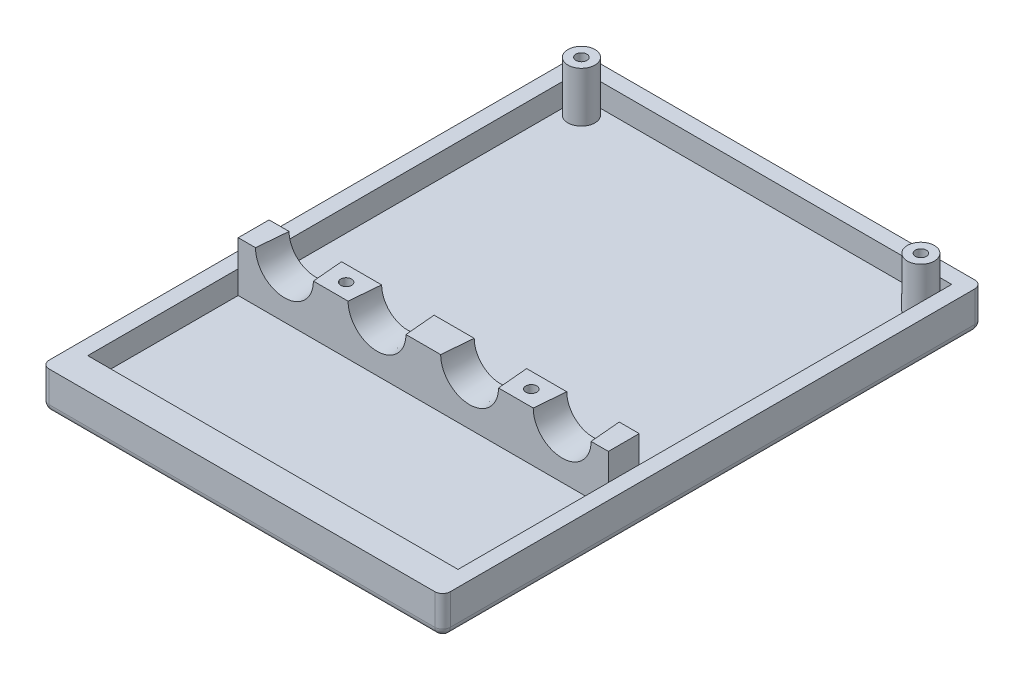
SolidWorks part; units mm, degrees
ref_plane "Front Plane" through (0, 0, 0) normal (0, 0, 1) x (1, 0, 0)
ref_plane "Top Plane" through (0, 0, 0) normal (0, 1, 0) x (1, 0, 0)
ref_plane "Right Plane" through (0, 0, 0) normal (1, 0, 0) x (0, 0, -1)
sketch "Sketch1" plane through (0, 0, 0) normal (0, 1, 0) x (1, 0, 0)
  line L1 (-41.275, -55.5625) -> (41.275, -55.5625)
  line L2 (-41.275, -55.5625) -> (-41.275, 55.5625)
  line L3 (-41.275, 55.5625) -> (41.275, 55.5625)
  line L4 (41.275, -55.5625) -> (41.275, 55.5625)
  line L5 (-41.275, -55.5625) -> (41.275, 55.5625) construction
  line L6 (-41.275, 55.5625) -> (41.275, -55.5625) construction
  point P0 (0, 0)
  dimension "D1" = 111.125
  dimension "D2" = 82.55
extrude "Boss-Extrude1" add sketch "Sketch1" along normal blind 7.9375
sketch "Sketch3" plane through (0, 7.9375, 0) normal (0, 1, 0) x (-1, 0, 0)
  line L0 (0, 0) -> (0, -1.5875) construction
  line L2 (38.1, 49.2125) -> (-38.1, 49.2125)
  line L3 (38.1, 49.2125) -> (38.1, -52.3875)
  line L4 (38.1, -52.3875) -> (-38.1, -52.3875)
  line L5 (-38.1, 49.2125) -> (-38.1, -52.3875)
  line L6 (38.1, 49.2125) -> (-38.1, -52.3875) construction
  line L7 (38.1, -52.3875) -> (-38.1, 49.2125) construction
  dimension "D1" = 1.5875
  dimension "D2" = 101.6
  dimension "D3" = 76.2
extrude "Cut-Extrude1" cut sketch "Sketch3" against normal offset from surface (4.7625 mm away) 3.175 up to face at (0, 0, 0)
sketch "Sketch4" plane through (0, 3.175, 0) normal (0, 1, 0) x (-1, 0, 0)
  line L0 (0, 49.2125) -> (0, 18.2563) construction
  line L1 (38.1, 49.2125) -> (-38.1, 49.2125) construction
  line L2 (38.1, 18.2563) -> (-38.1, 18.2563)
  line L3 (38.1, 18.2563) -> (38.1, 11.9063)
  line L4 (-38.1, 18.2563) -> (-38.1, 11.9063)
  line L5 (38.1, 11.9063) -> (-38.1, 11.9063)
  line L6 (38.1, -52.3875) -> (38.1, 49.2125) construction
  line L7 (-38.1, 49.2125) -> (-38.1, -52.3875) construction
  line L8 (0, -52.3875) -> (0, 11.9063) construction
  line L9 (-38.1, -52.3875) -> (38.1, -52.3875) construction
  line L10 (38.1, -52.3875) -> (38.1, 49.2125) construction
  line L11 (-38.1, -52.3875) -> (38.1, -52.3875) construction
  circle A0 centre (34.925, -49.2125) radius 2.7781
  circle A1 centre (-34.925, -49.2125) radius 2.7781
  dimension "D5" = 5.5562
  dimension "D1" = 30.9562
  dimension "D2" = 6.35
  dimension "D3" = 3.175
  dimension "D4" = 3.175
extrude "Boss-Extrude2" add sketch "Sketch4" along normal blind 4.7625
sketch "Sketch5" plane through (0, 7.9375, 0) normal (0, 1, 0) x (-1, 0, 0)
  line L0 (0, 11.9063) -> (0, 18.2563) construction
  line L1 (-38.1, 11.9063) -> (38.1, 11.9062) construction
  line L2 (38.1, 18.2563) -> (-38.1, 18.2563) construction
  line L3 (-38.1, 11.9062) -> (38.1, 11.9062) construction
  line L4 (38.0873, 18.2563) -> (-38.0873, 18.2563)
  line L5 (38.0873, 18.2563) -> (38.0873, 11.9062)
  line L6 (38.0873, 11.9062) -> (-38.0873, 11.9062)
  line L7 (-38.0873, 18.2563) -> (-38.0873, 11.9062)
  line L8 (38.0873, 18.2563) -> (-38.0873, 11.9062) construction
  line L9 (38.0873, 11.9062) -> (-38.0873, 18.2563) construction
  circle A0 centre (34.925, -49.2125) radius 2.7781
  circle A1 centre (-34.925, -49.2125) radius 2.7781
  point P6 (0, 15.0813)
  point P7 (0, 15.0813)
  dimension "D1" = 76.1746
extrude "Boss-Extrude3" add sketch "Sketch5" along normal blind 5.5499
sketch "Sketch6" plane through (0, 13.4874, 0) normal (0, 1, 0) x (-1, 0, 0)
  line L0 (0, 11.9062) -> (0, 18.2563) construction
  line L1 (-38.1, 11.9062) -> (38.1, 11.9062) construction
  line L2 (38.0873, 18.2563) -> (-38.0873, 18.2563) construction
  point P6 (0, 15.0813)
  point P7 (-9.525, 15.0813)
  point P8 (-28.575, 15.0813)
  point P9 (9.525, 15.0813)
  point P10 (28.575, 15.0813)
  dimension "D1" = 9.525
  dimension "D2" = 19.05
  dimension "D3" = 9.525
  dimension "D4" = 19.05
sketch "Sketch7" plane through (0, 0, 18.2563) normal (0, 0, 1) x (1, 0, 0)
  circle A0 centre (-28.575, 13.4874) radius 5.9531
  circle A1 centre (-9.525, 13.4874) radius 5.9531
  circle A2 centre (9.525, 13.4874) radius 5.9531
  circle A3 centre (28.575, 13.4874) radius 5.9531
  dimension "D1" = 11.9062
  dimension "D2" = 11.9062
  dimension "D3" = 11.9062
  dimension "D4" = 11.9062
extrude "Cut-Extrude2" cut sketch "Sketch7" against normal up to next (6.35 mm away) draft 5
fillet "Fillet1" radius 1.5875 8 edges at (-41.275, 0, 0) (-41.275, 3.9688, -55.5625) (0, 0, -55.5625) (41.275, 3.9688, -55.5625) (41.275, 0, 0) (41.275, 3.9688, 55.5625) (0, 0, 55.5625) (-41.275, 3.9688, 55.5625)
sketch "Sketch8"
sketch "Sketch9" plane through (0, 0, 0) normal (0, -1, 0) x (1, 0, 0)
  line L0 (-19.8716, 50.0609) -> (-23.3787, 50.0609)
  line L1 (-23.3787, 50.0609) -> (-23.3787, 49.463)
  line L2 (-23.3787, 49.463) -> (-24.789, 49.463)
  line L3 (-24.789, 49.463) -> (-24.789, 50.0609)
  line L4 (-24.789, 50.0609) -> (-28.2981, 50.0609)
  line L5 (-28.2981, 50.0609) -> (-28.2981, 49.463)
  line L6 (-28.2981, 49.463) -> (-30.1467, 49.463)
  line L7 (-30.1467, 49.463) -> (-30.1467, 48.2204)
  line L8 (-30.1467, 48.2204) -> (-30.8243, 48.2204)
  line L9 (-30.8243, 48.2204) -> (-30.8243, 47.5361)
  line L10 (-30.8243, 47.5361) -> (-31.942, 47.5361)
  line L11 (-31.942, 47.5361) -> (-31.942, 46.3625)
  line L12 (-31.942, 46.3625) -> (-32.6685, 46.3625)
  line L13 (-32.6685, 46.3625) -> (-32.6685, 45.7269)
  line L14 (-32.6685, 45.7269) -> (-33.2019, 45.7269)
  line L15 (-33.2019, 45.7269) -> (-33.2019, 43.2402)
  line L16 (-33.2019, 43.2402) -> (-33.7772, 43.2402)
  line L17 (-33.7772, 43.2402) -> (-33.7772, 42.0201)
  line L18 (-33.7772, 42.0201) -> (-36.2575, 42.0201)
  line L19 (-36.2575, 42.0201) -> (-36.2575, 41.5241)
  line L20 (-36.2575, 41.5241) -> (-36.8878, 41.5241)
  line L21 (-36.8878, 41.5241) -> (-36.8878, 37.8201)
  line L22 (-36.8878, 37.8201) -> (-36.2575, 37.8201)
  line L23 (-36.2575, 37.8201) -> (-36.2575, 37.3353)
  line L24 (-36.2575, 37.3353) -> (-34.4858, 37.3353)
  line L25 (-34.4858, 37.3353) -> (-34.4858, 32.325)
  line L26 (-34.4858, 32.325) -> (-33.7772, 32.325)
  line L27 (-33.7772, 32.325) -> (-33.7772, 31.6945)
  line L28 (-33.7772, 31.6945) -> (-33.2019, 31.6945)
  line L29 (-33.2019, 31.6945) -> (-33.2019, 30.5277)
  line L30 (-33.2019, 30.5277) -> (-31.942, 30.5277)
  line L31 (-31.942, 30.5277) -> (-31.942, 29.3143)
  line L32 (-31.942, 29.3143) -> (-32.572, 29.3143)
  line L33 (-32.572, 29.3143) -> (-32.572, 27.4612)
  line L34 (-32.572, 27.4612) -> (-33.2019, 27.4612)
  line L35 (-33.2019, 27.4612) -> (-33.2019, 26.3381)
  line L36 (-33.2019, 26.3381) -> (-30.8243, 26.3381)
  line L37 (-30.8243, 26.3381) -> (-30.8243, 27.4693)
  line L38 (-30.8243, 27.4693) -> (-30.1467, 27.4693)
  line L39 (-30.1467, 27.4693) -> (-30.1467, 28.0917)
  line L40 (-30.1467, 28.0917) -> (-29.5987, 28.0917)
  line L41 (-29.5987, 28.0917) -> (-29.5987, 27.4693)
  line L42 (-29.5987, 27.4693) -> (-28.909, 27.4693)
  line L43 (-28.909, 27.4693) -> (-28.909, 26.9037)
  line L44 (-28.909, 26.9037) -> (-28.2981, 26.9037)
  line L45 (-28.2981, 26.9037) -> (-28.2981, 25.6331)
  line L46 (-28.2981, 25.6331) -> (-25.9105, 25.6331)
  line L47 (-25.9105, 25.6331) -> (-25.9105, 25.0757)
  line L48 (-25.9105, 25.0757) -> (-22.7956, 25.0757)
  line L49 (-22.7956, 25.0757) -> (-22.7956, 25.6331)
  line L50 (-22.7956, 25.6331) -> (-20.372, 25.6331)
  line L51 (-20.372, 25.6331) -> (-20.372, 26.2684)
  line L52 (-20.372, 26.2684) -> (-19.8716, 26.2684)
  line L53 (-19.8716, 26.2684) -> (-19.8716, 26.9037)
  line L54 (-19.8716, 26.9037) -> (-19.0825, 26.9037)
  line L55 (-19.0825, 26.9037) -> (-19.0825, 27.4693)
  line L56 (-19.0825, 27.4693) -> (-17.993, 27.4693)
  line L57 (-17.993, 27.4693) -> (-17.993, 26.2684)
  line L58 (-17.993, 26.2684) -> (-16.0886, 26.2684)
  line L59 (-16.0886, 26.2684) -> (-16.0886, 29.3143)
  line L60 (-16.0886, 29.3143) -> (-16.6657, 29.3143)
  line L61 (-16.6657, 29.3143) -> (-16.6657, 30.5277)
  line L62 (-16.6657, 30.5277) -> (-14.8509, 30.5277)
  line L63 (-14.8509, 30.5277) -> (-14.8509, 32.325)
  line L64 (-14.8509, 32.325) -> (-14.2519, 32.325)
  line L65 (-14.2519, 32.325) -> (-14.2519, 35.9948)
  line L66 (-14.2519, 35.9948) -> (-13.6584, 35.9948)
  line L67 (-13.6584, 35.9948) -> (-13.6584, 37.3353)
  line L68 (-13.6584, 37.3353) -> (-11.8844, 37.3353)
  line L69 (-11.8844, 37.3353) -> (-11.8844, 37.8201)
  line L70 (-11.8844, 37.8201) -> (-11.2802, 37.8201)
  line L71 (-11.2802, 37.8201) -> (-11.2802, 41.5241)
  line L72 (-11.2802, 41.5241) -> (-11.8844, 41.5241)
  line L73 (-11.8844, 41.5241) -> (-11.8844, 42.0201)
  line L74 (-11.8844, 42.0201) -> (-14.2519, 42.0201)
  line L75 (-14.2519, 42.0201) -> (-14.2519, 43.2402)
  line L76 (-14.2519, 43.2402) -> (-14.8509, 43.2402)
  line L77 (-14.8509, 43.2402) -> (-14.8509, 45.7269)
  line L78 (-14.8509, 45.7269) -> (-15.4335, 45.7269)
  line L79 (-15.4335, 45.7269) -> (-15.4335, 46.3625)
  line L80 (-15.4335, 46.3625) -> (-16.0886, 46.3625)
  line L81 (-16.0886, 46.3625) -> (-16.0886, 47.5361)
  line L82 (-16.0886, 47.5361) -> (-17.3, 47.5361)
  line L83 (-17.3, 47.5361) -> (-17.3, 48.2204)
  line L84 (-17.3, 48.2204) -> (-17.993, 48.2204)
  line L85 (-17.993, 48.2204) -> (-17.993, 49.463)
  line L86 (-17.993, 49.463) -> (-19.8716, 49.463)
  line L87 (-19.8716, 49.463) -> (-19.8716, 50.0609)
  line L88 (-16.6657, 42.6636) -> (-17.993, 42.6636)
  line L89 (-17.993, 42.6636) -> (-17.993, 43.2402)
  line L90 (-17.993, 43.2402) -> (-19.8716, 43.2402)
  line L91 (-19.8716, 43.2402) -> (-19.8716, 43.8326)
  line L92 (-19.8716, 43.8326) -> (-21.6, 43.8326)
  line L93 (-21.6, 43.8326) -> (-21.6, 43.2402)
  line L94 (-21.6, 43.2402) -> (-22.2049, 43.2402)
  line L95 (-22.2049, 43.2402) -> (-22.2049, 42.6636)
  line L96 (-22.2049, 42.6636) -> (-22.7956, 42.6636)
  line L97 (-22.7956, 42.6636) -> (-22.7956, 41.5241)
  line L98 (-22.7956, 41.5241) -> (-25.2305, 41.5241)
  line L99 (-25.2305, 41.5241) -> (-25.2305, 42.6636)
  line L100 (-25.2305, 42.6636) -> (-25.9105, 42.6636)
  line L101 (-25.9105, 42.6636) -> (-25.9105, 43.2402)
  line L102 (-25.9105, 43.2402) -> (-26.5628, 43.2402)
  line L103 (-26.5628, 43.2402) -> (-26.5628, 43.8326)
  line L104 (-26.5628, 43.8326) -> (-28.2981, 43.8326)
  line L105 (-28.2981, 43.8326) -> (-28.2981, 43.2402)
  line L106 (-28.2981, 43.2402) -> (-30.1467, 43.2402)
  line L107 (-30.1467, 43.2402) -> (-30.1467, 42.6636)
  line L108 (-30.1467, 42.6636) -> (-31.4448, 42.6636)
  line L109 (-31.4448, 42.6636) -> (-31.4448, 41.5241)
  line L110 (-31.4448, 41.5241) -> (-31.942, 41.5241)
  line L111 (-31.942, 41.5241) -> (-31.942, 40.9226)
  line L112 (-31.942, 40.9226) -> (-32.6685, 40.9226)
  line L113 (-32.6685, 40.9226) -> (-32.6685, 38.4611)
  line L114 (-32.6685, 38.4611) -> (-31.942, 38.4611)
  line L115 (-31.942, 38.4611) -> (-31.942, 37.8201)
  line L116 (-31.942, 37.8201) -> (-30.7958, 37.8201)
  line L117 (-30.7958, 37.8201) -> (-30.7958, 37.3353)
  line L118 (-30.7958, 37.3353) -> (-30.1467, 37.3353)
  line L119 (-30.1467, 37.8201) -> (-25.9105, 37.8201)
  line L120 (-25.9105, 37.8201) -> (-25.9105, 38.4611)
  line L121 (-25.9105, 38.4611) -> (-22.2049, 38.4611)
  line L122 (-22.2049, 38.4611) -> (-22.2049, 37.8201)
  line L123 (-22.2049, 37.8201) -> (-17.993, 37.8201)
  line L124 (-17.993, 37.8201) -> (-17.993, 37.3353)
  line L125 (-17.993, 37.3353) -> (-17.3, 37.3353)
  line L126 (-17.3, 37.3353) -> (-17.3, 37.8201)
  line L127 (-17.3, 37.8201) -> (-16.0886, 37.8201)
  line L128 (-16.0886, 37.8201) -> (-16.0886, 38.4611)
  line L129 (-16.0886, 38.4611) -> (-15.4335, 38.4611)
  line L130 (-15.4335, 38.4611) -> (-15.4335, 40.9226)
  line L131 (-15.4335, 40.9226) -> (-16.0886, 40.9226)
  line L132 (-16.0886, 40.9226) -> (-16.0886, 41.5241)
  line L133 (-16.0886, 41.5241) -> (-16.6657, 41.5241)
  line L134 (-16.6657, 41.5241) -> (-16.6657, 42.6636)
  line L135 (-17.3, 38.4611) -> (-19.8716, 38.4611)
  line L136 (-19.8716, 38.4611) -> (-19.8716, 39.0562)
  line L137 (-19.8716, 39.0562) -> (-20.372, 39.0562)
  line L138 (-20.372, 39.0562) -> (-20.372, 39.6742)
  line L139 (-20.372, 39.6742) -> (-21.0154, 39.6742)
  line L140 (-21.0154, 39.6742) -> (-21.0154, 40.2921)
  line L141 (-21.0154, 40.2921) -> (-21.6, 40.2921)
  line L142 (-21.6, 40.2921) -> (-21.6, 41.5241)
  line L143 (-21.6, 41.5241) -> (-21.0154, 41.5241)
  line L144 (-21.0154, 41.5241) -> (-21.0154, 42.0201)
  line L145 (-21.0154, 42.0201) -> (-19.1927, 42.0201)
  line L146 (-19.1927, 42.0201) -> (-19.1927, 41.5241)
  line L147 (-19.1927, 41.5241) -> (-17.993, 41.5241)
  line L148 (-17.993, 41.5241) -> (-17.993, 40.2921)
  line L149 (-17.993, 40.2921) -> (-17.3, 40.2921)
  line L150 (-17.3, 40.2921) -> (-17.3, 38.4611)
  line L151 (-26.5628, 41.5241) -> (-26.5628, 40.2921)
  line L152 (-26.5628, 40.2921) -> (-27.12, 40.2921)
  line L153 (-27.12, 40.2921) -> (-27.12, 39.6742)
  line L154 (-27.12, 39.6742) -> (-27.7379, 39.6742)
  line L155 (-27.7379, 39.6742) -> (-27.7379, 39.0562)
  line L156 (-27.7379, 39.0562) -> (-28.2981, 39.0562)
  line L157 (-28.2981, 39.0562) -> (-28.2981, 38.4611)
  line L158 (-28.2981, 38.4611) -> (-30.7958, 38.4611)
  line L159 (-30.7958, 38.4611) -> (-30.7958, 40.2921)
  line L160 (-30.7958, 40.2921) -> (-30.1467, 40.2921)
  line L161 (-30.1467, 40.2921) -> (-30.1467, 41.5241)
  line L162 (-30.1467, 41.5241) -> (-28.909, 41.5241)
  line L163 (-28.909, 41.5241) -> (-28.909, 42.1435)
  line L164 (-28.909, 42.1435) -> (-27.12, 42.1435)
  line L165 (-27.12, 42.1435) -> (-27.12, 41.5241)
  line L166 (-27.12, 41.5241) -> (-26.5628, 41.5241)
  line L167 (-21.0154, 47.5361) -> (-21.0154, 46.3625)
  line L168 (-21.0154, 46.3625) -> (-21.6, 46.3625)
  line L169 (-21.6, 46.3625) -> (-21.6, 45.7269)
  line L170 (-21.6, 45.7269) -> (-26.5628, 45.7269)
  line L171 (-26.5628, 45.7269) -> (-26.5628, 46.3625)
  line L172 (-26.5628, 46.3625) -> (-27.12, 46.3625)
  line L173 (-27.12, 46.3625) -> (-27.12, 47.5361)
  line L174 (-27.12, 47.5361) -> (-26.5628, 47.5361)
  line L175 (-26.5628, 47.5361) -> (-26.5628, 46.9493)
  line L176 (-26.5628, 46.9493) -> (-25.9105, 46.9493)
  line L177 (-25.9105, 46.9493) -> (-25.9105, 46.3625)
  line L178 (-25.9105, 46.3625) -> (-22.2049, 46.3625)
  line L179 (-22.2049, 46.3625) -> (-22.2049, 46.9493)
  line L180 (-22.2049, 46.9493) -> (-21.6, 46.9493)
  line L181 (-21.6, 46.9493) -> (-21.6, 47.5361)
  line L182 (-21.6, 47.5361) -> (-21.0154, 47.5361)
  line L183 (-17.3, 31.6945) -> (-17.3, 30.5277)
  line L184 (-17.3, 30.5277) -> (-17.993, 30.5277)
  line L185 (-17.993, 30.5277) -> (-17.993, 31.6945)
  line L186 (-17.993, 31.6945) -> (-17.3, 31.6945)
  line L191 (-18.5889, 32.325) -> (-18.5889, 33.0324)
  line L192 (-18.5889, 33.0324) -> (-19.0825, 33.0324)
  line L193 (-19.0825, 33.0324) -> (-19.0825, 34.2235)
  line L194 (-19.0825, 34.2235) -> (-20.372, 34.2235)
  line L195 (-20.372, 34.2235) -> (-20.372, 35.4554)
  line L196 (-20.372, 35.4554) -> (-21.0154, 35.4554)
  line L197 (-21.0154, 35.4554) -> (-21.0154, 35.9948)
  line L198 (-21.0154, 35.9948) -> (-22.7956, 35.9948)
  line L199 (-22.7956, 35.9948) -> (-22.7956, 36.6046)
  line L200 (-22.7956, 36.6046) -> (-25.9105, 36.6046)
  line L201 (-25.9105, 36.6046) -> (-25.9105, 35.9948)
  line L202 (-25.9105, 35.9948) -> (-27.12, 35.9948)
  line L203 (-27.12, 35.9948) -> (-27.12, 35.4554)
  line L204 (-27.12, 35.4554) -> (-28.2981, 35.4554)
  line L205 (-28.2981, 35.4554) -> (-28.2981, 34.2235)
  line L206 (-28.2981, 34.2235) -> (-28.909, 34.2235)
  line L207 (-28.909, 34.2235) -> (-28.909, 33.0324)
  line L208 (-28.909, 33.0324) -> (-28.2981, 33.0324)
  line L209 (-28.2981, 33.0324) -> (-28.2981, 33.6279)
  line L210 (-28.2981, 33.6279) -> (-27.12, 33.6279)
  line L211 (-27.12, 33.6279) -> (-27.12, 34.8394)
  line L212 (-27.12, 34.8394) -> (-26.5153, 34.8394)
  line L213 (-26.5153, 34.8394) -> (-26.5153, 34.2337)
  line L214 (-26.5153, 34.2337) -> (-25.2305, 34.2337)
  line L215 (-25.2305, 34.2337) -> (-25.2305, 35.4554)
  line L216 (-25.2305, 35.4554) -> (-24.789, 35.4554)
  line L217 (-24.789, 35.4554) -> (-24.789, 34.2337)
  line L218 (-24.789, 34.2337) -> (-24.0327, 34.2337)
  line L219 (-24.0327, 34.2337) -> (-24.0327, 35.4554)
  line L220 (-24.0327, 35.4554) -> (-22.7956, 35.4554)
  line L221 (-22.7956, 35.4554) -> (-22.7956, 34.2337)
  line L222 (-22.7956, 34.2337) -> (-22.2049, 34.2337)
  line L223 (-22.2049, 34.2337) -> (-22.2049, 35.4554)
  line L224 (-22.2049, 35.4554) -> (-21.6, 35.4554)
  line L225 (-21.6, 35.4554) -> (-21.6, 34.8445)
  line L226 (-21.6, 34.8445) -> (-21.0154, 34.8445)
  line L227 (-21.0154, 34.8445) -> (-21.0154, 33.6279)
  line L228 (-21.0154, 33.6279) -> (-20.372, 33.6279)
  line L229 (-20.372, 33.6279) -> (-20.372, 32.325)
  line L230 (-20.372, 32.325) -> (-18.5889, 32.325)
  line L235 (-28.909, 33.0324) -> (-28.9617, 33.0283)
  line L236 (-20.4654, 29.3143) -> (-20.4654, 27.4693)
  line L237 (-20.4654, 27.4693) -> (-22.2049, 27.4693)
  line L238 (-22.2049, 27.4693) -> (-22.2049, 29.3143)
  line L239 (-22.2049, 29.3143) -> (-22.7956, 29.3143)
  line L240 (-22.7956, 29.3143) -> (-22.7956, 29.9632)
  line L241 (-22.7956, 29.9632) -> (-21.0154, 29.9632)
  line L242 (-21.0154, 29.9632) -> (-21.0154, 29.3143)
  line L243 (-21.0154, 29.3143) -> (-20.4654, 29.3143)
  line L251 (-24.789, 26.2684) -> (-24.789, 27.4693)
  line L252 (-24.789, 27.4693) -> (-25.9105, 27.4693)
  line L253 (-25.9105, 27.4693) -> (-25.9105, 26.8689)
  line L254 (-25.9105, 26.8689) -> (-25.3498, 26.8689)
  line L255 (-25.3498, 26.8689) -> (-25.3498, 26.2684)
  line L256 (-25.3498, 26.2684) -> (-24.789, 26.2684)
  line L257 (-25.2305, 29.88) -> (-25.2305, 29.3143)
  line L258 (-25.2305, 29.3143) -> (-26.5153, 29.3143)
  line L259 (-26.5153, 29.3143) -> (-26.5153, 28.701)
  line L260 (-26.5153, 28.701) -> (-28.2981, 28.701)
  line L264 (-28.2981, 29.3143) -> (-27.12, 29.3143)
  line L265 (-27.12, 29.3143) -> (-27.12, 29.88)
  line L266 (-27.12, 29.88) -> (-25.2305, 29.88)
  line L269 (-28.2981, 28.701) -> (-28.2981, 29.3143)
  line L270 (-30.1467, 37.3353) -> (-30.1467, 37.8201)
extrude "Cut-Extrude6" cut sketch "Sketch9" against normal blind 0.7937 contours L86 L87 L0 L1 L2 L3 L4 L5 L6 L7 L8 L9 L10 L11 L12 L13 L14 L15 L16 L17 L18 L19 L20 L21 L22 L23 L24 L25 L26 L27 L28 L29 L30 L31 L32 L33 L34 L35 L36 L37 L38 L39 L40 L41 L42 L43 L44 L45 L46 L47 L48 | L166 L165 L164 L163 L162 L161 L160 L159 L158 L157 L156 L155 L154 L153 L152 L151 | L150 L149 L148 L147 L146 L145 L144 L143 L142 L141 L140 L139 L138 L137 L136 L135
sketch "Sketch10" plane through (0, 0.7937, 0) normal (0, -1, 0) x (1, 0, 0)
  line L1 (-17.993, 31.6945) -> (-18.5889, 31.6945)
  line L2 (-17.993, 31.6945) -> (-17.993, 32.325)
  line L3 (-17.993, 32.325) -> (-18.5889, 32.325)
  line L4 (-18.5889, 31.6945) -> (-18.5889, 32.325)
  line L5 (-29.5987, 28.0917) -> (-28.2981, 28.0917)
  line L6 (-29.5987, 28.0917) -> (-29.5987, 28.701)
  line L7 (-29.5987, 28.701) -> (-28.2981, 28.701)
  line L8 (-28.2981, 28.0917) -> (-28.2981, 28.701)
  line L9 (-24.0864, 26.2684) -> (-22.7956, 26.2684)
  line L10 (-24.0864, 26.2684) -> (-24.0864, 25.6331)
  line L11 (-24.0864, 25.6331) -> (-22.7956, 25.6331)
  line L12 (-22.7956, 26.2684) -> (-22.7956, 25.6331)
  line L13 (-22.7956, 26.2684) -> (-22.2049, 26.2684)
  line L14 (-22.7956, 26.2684) -> (-22.7956, 27.4693)
  line L15 (-22.7956, 27.4693) -> (-22.2049, 27.4693)
  line L16 (-22.2049, 26.2684) -> (-22.2049, 27.4693)
extrude "Boss-Extrude10" add sketch "Sketch10" along normal blind 0.7937 separate body contours L5 L8 L7 L6 | L12 L9 L10 L11 | L13 L16 L15 L14 | L4 L1 L2 L3
sketch "HoleLocations" plane through (0, 13.4874, 0) normal (0, 1, 0) x (-1, 0, 0)
  point P0 (19.05, 15.0813)
  point P1 (-19.05, 15.0813)
hole_wizard "#4-40 Tapped Hole4" positions "Sketch27" profile "Sketch26" tap size "#4-40" standard "Ansi Inch"
sketch "Sketch27" plane through (0, 13.4874, 0) normal (0, 1, 0) x (-1, 0, 0)
  point P0 (-19.05, 15.0813)
  point P7 (19.05, 15.0813)
  point P17 (34.925, -49.2125)
  point P20 (-34.925, -49.2125)
sketch "Sketch26" plane through (19.05, 13.4874, 15.0813) normal (1, 0, 0) x (0, 0, 1)
  line L0 (0, 0) -> (0, 6.2672)
  line L1 (0, 6.2672) -> (1.1303, 5.588)
  line L2 (1.1303, 5.588) -> (1.1303, 0)
  line L5 (1.1303, 0) -> (0, 0)
  line L10 (0, 6.2672) -> (-1.1303, 5.588) construction
  line L11 (0, -6.35) -> (0, 107.95) construction
  dimension "Tap Drill Dia." = 2.2606
  dimension "Tap Drill Depth" = 5.588
  dimension "Drill Angle" = 118
cosmetic thread "Hole Thread10" parameters "D1"=5.588, "D2"=2.8448
cosmetic thread "Hole Thread11" parameters "D1"=5.588, "D2"=2.8448
cosmetic thread "Hole Thread12" parameters "D1"=5.588, "D2"=2.8448
cosmetic thread "Hole Thread13" parameters "D1"=5.588, "D2"=2.8448
